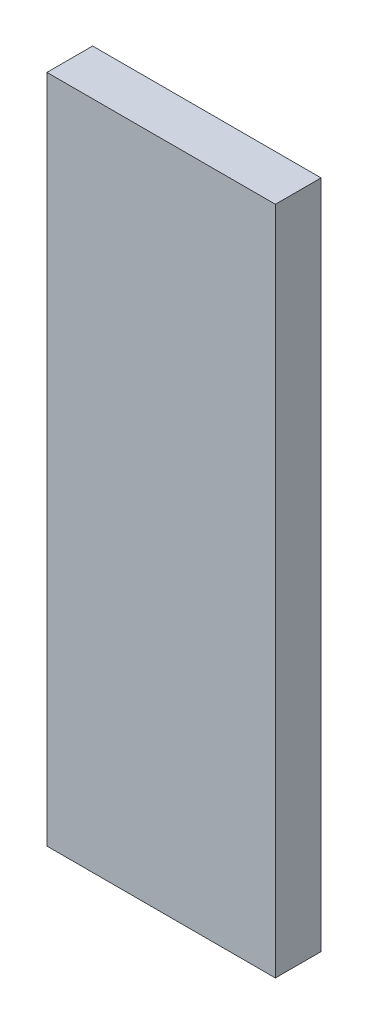
SolidWorks part; units mm, degrees
material "Cedar"
ref_plane "Front Plane" through (0, 0, 0) normal (0, 0, 1) x (1, 0, 0)
ref_plane "Top Plane" through (0, 0, 0) normal (0, 1, 0) x (1, 0, 0)
ref_plane "Right Plane" through (0, 0, 0) normal (1, 0, 0) x (0, 0, -1)
sketch "Sketch1" plane through (0, 0, 0) normal (0, 0, 1) x (1, 0, 0)
  line L1 (-7.5, -22) -> (7.5, -22)
  line L2 (-7.5, -22) -> (-7.5, 22)
  line L3 (-7.5, 22) -> (7.5, 22)
  line L4 (7.5, -22) -> (7.5, 22)
  line L5 (-7.5, -22) -> (7.5, 22) construction
  line L6 (-7.5, 22) -> (7.5, -22) construction
  point P0 (0, 0)
  dimension "D1" = 15
  dimension "D2" = 44
extrude "Boss-Extrude1" add sketch "Sketch1" along normal blind 3
